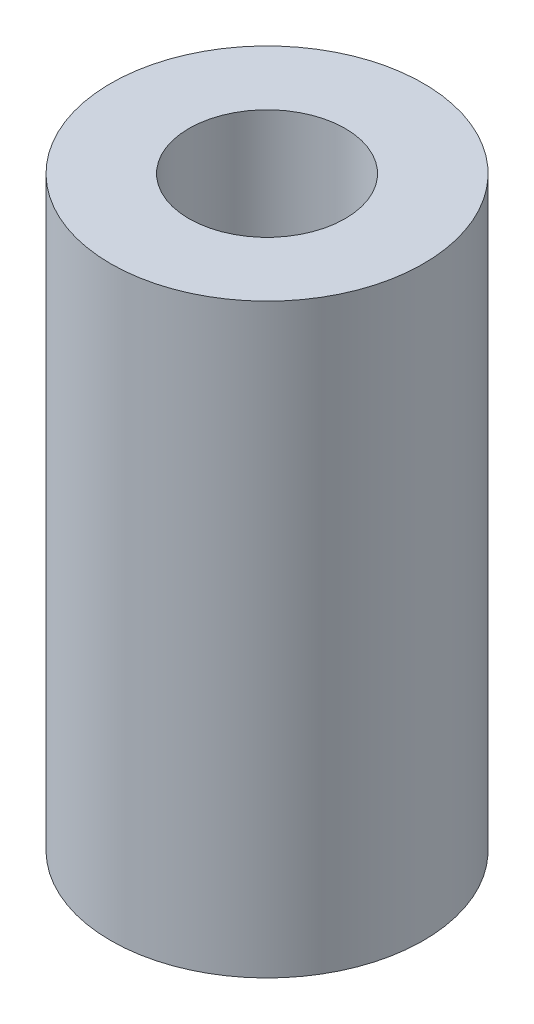
SolidWorks part; units mm, degrees
ref_plane "Front Plane" through (0, 0, 0) normal (0, 0, 1) x (1, 0, 0)
ref_plane "Top Plane" through (0, 0, 0) normal (0, 1, 0) x (1, 0, 0)
ref_plane "Right Plane" through (0, 0, 0) normal (1, 0, 0) x (0, 0, -1)
sketch "Sketch1" plane through (0, 0, 0) normal (0, 1, 0) x (1, 0, 0)
  circle A0 centre (0, 0) radius 8
  circle A1 centre (0, 0) radius 4
  dimension "D1" = 16
  dimension "D2" = 8
extrude "Boss-Extrude1" add sketch "Sketch1" along normal blind 30
